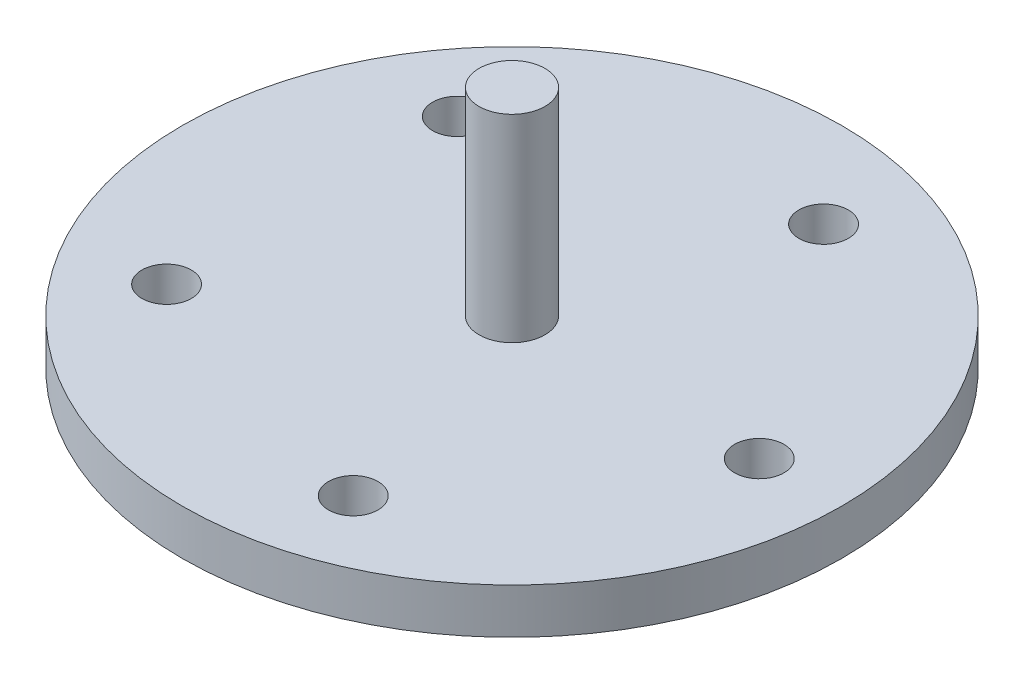
SolidWorks part; units mm, degrees
material "Malleable Cast Iron"
ref_plane "Front Plane" through (0, 0, 0) normal (0, 0, 1) x (1, 0, 0)
ref_plane "Top Plane" through (0, 0, 0) normal (0, 1, 0) x (1, 0, 0)
ref_plane "Right Plane" through (0, 0, 0) normal (1, 0, 0) x (0, 0, -1)
sketch "Sketch1" plane through (0, 0, 0) normal (0, 1, 0) x (1, 0, 0)
  circle A0 centre (0, 0) radius 40
extrude "Boss-Extrude1" add sketch "Sketch1" along normal blind 5.5
sketch "Sketch2" plane through (0, 5.5, 0) normal (0, 1, 0) x (1, 0, 0)
  circle A0 centre (30, 0) radius 3
  dimension "D1" = 30
extrude "Cut-Extrude1" cut sketch "Sketch2" against normal through all
pattern_circular "CirPattern1" count 5 over 360 about axis through (0, 0, 0) along (0, 1, 0) of "Cut-Extrude1"
sketch "Sketch3" plane through (0, 5.5, 0) normal (0, 1, 0) x (1, 0, 0)
  circle A0 centre (0, 0) radius 4
  dimension "D1" = 8
extrude "Boss-Extrude2" add sketch "Sketch3" along normal blind 24
